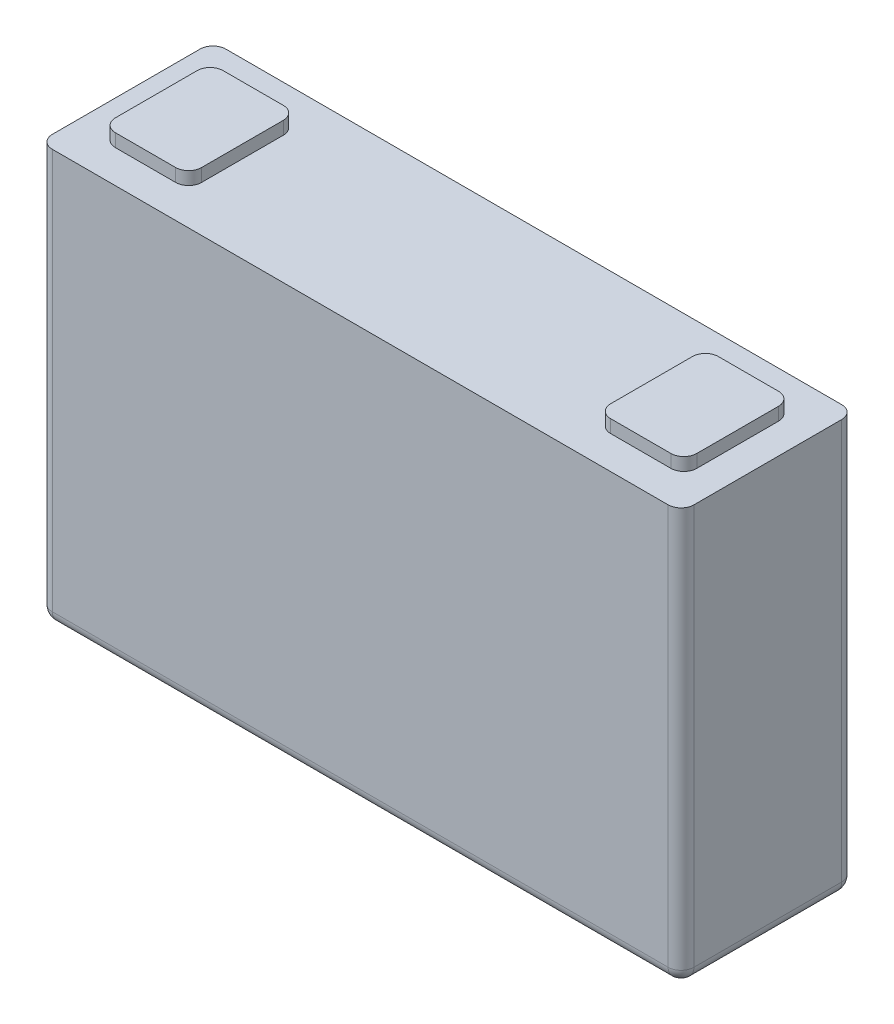
SolidWorks part; units mm, degrees
ref_plane "Front Plane" through (0, 0, 0) normal (0, 0, 1) x (1, 0, 0)
ref_plane "Top Plane" through (0, 0, 0) normal (0, 1, 0) x (1, 0, 0)
ref_plane "Right Plane" through (0, 0, 0) normal (1, 0, 0) x (0, 0, -1)
sketch "Sketch1" plane through (0, 0, 0) normal (0, 0, 1) x (1, 0, 0)
  line L1 (-74.5, 48) -> (74.5, 48)
  line L2 (-74.5, 48) -> (-74.5, -48)
  line L3 (-74.5, -48) -> (74.5, -48)
  line L4 (74.5, 48) -> (74.5, -48)
  dimension "D1" = 149
  dimension "D2" = 96
  dimension "D3" = 74.5
  dimension "D4" = 48
extrude "Boss-Extrude1" add sketch "Sketch1" along normal mid plane 40.3
sketch "Sketch2" plane through (0, 48, 0) normal (0, 1, 0) x (1, 0, 0)
  line L0 (0, 52.3351) -> (0, -40.6323) construction
  line L1 (-67.5, 12.5) -> (-47.5, 12.5)
  line L2 (-67.5, 12.5) -> (-67.5, -12.5)
  line L3 (-67.5, -12.5) -> (-47.5, -12.5)
  line L4 (-47.5, 12.5) -> (-47.5, -12.5)
  line L5 (-57.5, 12.5) -> (-57.5, -12.5) construction
  line L6 (57.5, 12.5) -> (57.5, -12.5) construction
  line L7 (67.5, -12.5) -> (47.5, -12.5)
  line L8 (47.5, 12.5) -> (47.5, -12.5)
  line L9 (67.5, 12.5) -> (47.5, 12.5)
  line L10 (67.5, 12.5) -> (67.5, -12.5)
  point P7 (-47.5, 0)
  point P10 (-57.5, 0)
  dimension "D1" = 20
  dimension "D2" = 25
  dimension "D3" = 57.5
extrude "Boss-Extrude2" add sketch "Sketch2" along normal mid plane 6
fillet "Fillet1" radius 3 4 edges at (-74.5, 0, 20.15) (-74.5, 0, -20.15) (74.5, 0, -20.15) (74.5, 0, 20.15)
fillet "Fillet2" radius 3 8 edges at (-73.6213, -48, 19.2713) (0, -48, 20.15) (73.6213, -48, 19.2713) (74.5, -48, 0) (73.6213, -48, -19.2713) (0, -48, -20.15) (-73.6213, -48, -19.2713) (-74.5, -48, 0)
fillet "Fillet3" radius 3 8 edges at (47.5, 49.5, -12.5) (47.5, 49.5, 12.5) (67.5, 49.5, -12.5) (67.5, 49.5, 12.5) (-67.5, 49.5, 12.5) (-47.5, 49.5, 12.5) (-47.5, 49.5, -12.5) (-67.5, 49.5, -12.5)
